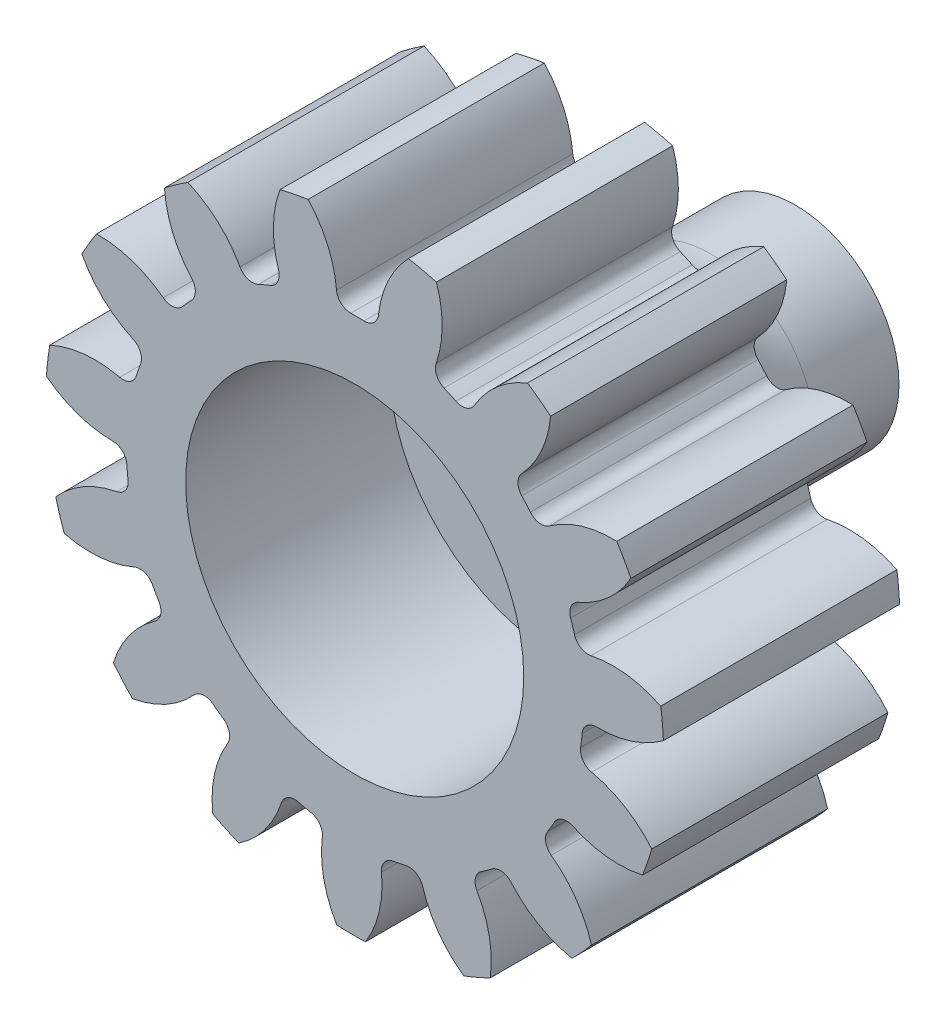
SolidWorks part; units mm, degrees
material "ABS"
ref_plane "Front" through (0, 0, 0) normal (0, 0, 1) x (1, 0, 0)
ref_plane "Top" through (0, 0, 0) normal (0, 1, 0) x (1, 0, 0)
ref_plane "Right" through (0, 0, 0) normal (1, 0, 0) x (0, 0, -1)
sketch "Sketch3" plane through (0, 0, 0) normal (0, 0, 1) x (1, 0, 0)
  circle A0 centre (0, 0) radius 21.59
  dimension "od" = 43.18
extrude "gearBody" add sketch "Sketch3" along normal blind 11
sketch "Sketch2" plane through (0, 0, 0) normal (0, 0, 1) x (1, 0, 0)
  line L0 (0, 0) -> (17.0393, 7.0579) construction
  line L1 (22.0105, -8.0941) -> (0, 0) construction
  line L2 (0, 0) -> (36.3143, 0) construction
  line L3 (19.0486, -0.229) -> (18.5878, -4.1711) construction
  line L5 (18.8182, -2.2) -> (0, 0) construction
  line L7 (0, 0) -> (18.4432, 0) construction
  arc A0 (18.4395, -0.3701) -> (18.0276, -3.8932) centre (0, 0) ccw construction
  arc A1 (21.5666, 1.0048) -> (20.7532, -5.9524) centre (0, 0) ccw construction
  arc A2 (19.0486, -0.229) -> (18.5878, -4.1711) centre (0, 0) ccw construction
  arc A3 (15.7838, -2.3046) -> (15.8898, -1.3984) centre (0, 0) ccw
  arc A4 (22.0105, -8.0941) -> (16.5506, -3.4102) centre (14.9518, -10.798) ccw
  arc A5 (22.0105, -8.0941) -> (23.2839, 2.7987) centre (0, 0) ccw
  arc A6 (23.2839, 2.7987) -> (16.8909, -0.4995) centre (17.0393, 7.0579) cw
  arc A7 (15.8898, -1.3984) -> (16.8909, -0.4995) centre (16.8715, -1.4848) cw
  arc A8 (16.5506, -3.4102) -> (15.7838, -2.3046) centre (16.759, -2.4469) cw
  point P6 (23.2839, 2.7987)
  point P22 (22.0105, -8.0941)
  dimension "baseDia" = 36.8864
  dimension "od" = 43.18
  dimension "pd" = 38.1
  dimension "rd" = 31.9024
  dimension "rFillet" = 0.9855
  dimension "pointX" = 23.2839
  dimension "pointY" = 2.7987
  dimension "CTT" = 3.9421
  dimension "flankCenterAngle" = 22.5
extrude "toothCut" cut sketch "Sketch2" along normal through all
pattern_circular "CirPattern1" count 15 over 360 about axis through (0, 0, 0) along (0, 0, 1) of "toothCut"
scale "Scale1" scale about centroid uniform scaling no x scale factor 0.666667 y scale factor 0.666667 z scale factor 1
sketch "hub1Dia" plane through (0, 0, 0) normal (0, 0, -1) x (-1, 0, 0)
  circle A0 centre (0, 0) radius 12.7
  dimension "hub1Dia" = 25.4
sketch "hub2Dia" plane through (0, 0, 11) normal (0, 0, 1) x (1, 0, 0)
  circle A0 centre (0, 0) radius 12.7
  dimension "hub2dia" = 25.4
sketch "boreDia" plane through (0, 0, 0) normal (0, 0, 1) x (1, 0, 0)
  circle A0 centre (0, 0) radius 7.874
  dimension "boreDia" = 15.748
extrude "bore" cut sketch "boreDia" against normal mid plane 25400
sketch "Sketch4" plane through (0, 0, 0) normal (1, 0, 0) x (0, 0, -1)
  line L0 (9.525, 0) -> (-1.524, 0)
  line L1 (-1.524, 0) -> (-1.524, 7.874)
  line L2 (-1.524, 7.874) -> (0, 7.874)
  line L3 (0, 8.1454) -> (0, 11.133) construction
  line L4 (0, 7.874) -> (0, 10.414)
  line L7 (5.588, 4.826) -> (9.525, 4.826)
  line L8 (9.525, 4.826) -> (9.525, 0)
  line L9 (0, 0) -> (18.4907, 0) construction
  arc A0 (0, 10.414) -> (5.588, 4.826) centre (5.588, 10.414) ccw
  dimension "D2" = 5.588
  dimension "D1" = 15.748
  dimension "D3" = 1.524
  dimension "D5" = 9.652
  dimension "D6" = 9.525
revolve "Revolve1" add sketch "Sketch4" angle 360 about L9
sketch "Sketch5" plane through (0, 0, -9.525) normal (0, 0, -1) x (-1, 0, 0)
  circle A0 centre (0, 0) radius 4.1
  dimension "D1" = 8.2
extrude "Cut-Extrude1" cut sketch "Sketch5" against normal blind 5.3
equation "\"Motor_OD\" = 54.4mm"
equation "\"Motor_Length\" = 401mm"
equation "\"Aft_Section_Length\" = 32in"
equation "\"Mid_Coupler_Length\" = 12in"
equation "\"AB_Coupler_OD_Length\"= 1in"
equation "\"AB_Coupling_Section_Length\"= 0.375in"
equation "\"AB_Coupler_Length\"= \"AB_Coupler_OD_Length\" + \"AB_Coupling_Section_Length\" * 2"
equation "\"Cutout_Angle\" = 60"
equation "\"AB_Paddle_Height\" = 0.375in"
equation "\"AB_Coupler_Num_Screws\"= 4"
equation "\"Num_Cutouts\" = 4"
equation "\"AB_Coupler_OD\"= 4.024in"
equation "\"AB_Coupler_ID\"= 3.7in"
equation "\"AB_Coupler_Surface_Diameter\"= 3.899in"
equation "\"AB_Coupling_Screw_Diameter\"= 4.5mm"
equation "\"AB_Central_Bushing_Length\" = 0.75in"
equation "\"Lead_Screw_Dist\" = 2in"
equation "\"Lead_Screw_Diam\" = 0.375in"
equation "\"Lead_Screw_Length\" = \"Mid_Coupler_Length\" + 2*0.375in + 2*0.5in"
equation "\"Paddle_Pin_Offset\" = 0.25in"
equation "\"Paddle_Pin_Radius\" = 2.25*2/3in"
equation "\"Paddle_Gear_OD\" = 3.2in"
equation "\"Fwd_BKHD_From_Top\" = 18in"
equation "\"Body_Tube_OD\"= 4.024in"
equation "\"Body_Tube_ID\"= 3.90in"
equation "\"Coupler_OD\" = 3.899in"
equation "\"Coupler_ID\" = 3.755in"
equation "\"Fwd_Section_Length\" = 20in"
equation "\"Mid_Section_Length\" = 4in"
equation "\"Aft_Upper_Tube_Length\" = 10in"
equation "\"Aft_Lower_Tube_Length\" = 18in"
equation "\"Nosecone_Coupler_Length\" = 5in"
equation "\"Avionics_Bulkhead_Thickness\" = 0.25in"
equation "\"Avionics_Bulkhead_Lip\" = 0.125in"
equation "\"Avionics_Board_Length\" = \"Mid_Coupler_Length\" - 2*\"Avionics_Bulkhead_Lip\""
equation "\"Lead_Screw_Hole_Diam\" = 0.386in"
equation "\"Centering_Ring_Cutout_Dia\"= 1in"
equation "\"Fin_Thickness\" = 0.118in"
equation "\"Airbrakes_Wire_Hole_Dist\" = 1.1*2/3in"
equation "\"Airbrakes_Wire_Hole_Dia\" = 0.25in"
equation "\"Drive_Gear_OD\" = 1.7*2/3in"
equation "\"DB9_Hole_Dist\" = 25mm"
equation "\"DB9_Relief_Width\" = 0.47in"
equation "\"DB9_Relief_Hole_Offset\" = 0.09in"
equation "\"Servo_Gear_Offset\" = 0.5in"
equation "\"Mounting_Bracket_Centerhole_DIA\" = 0.4in"
equation "\"Drive_Gear_Shaft_DIA\" = \"Mounting_Bracket_Centerhole_DIA\" - 0.02in"
equation "\"Drive_Gear_Fillet\" = 0.22in"
equation "\"Drive_Gear_ID\" = 0.62in"
equation "\"M3_Thread_Clearance\" = 3.8mm"
equation "\"M3_Screw_Head_Diam\" = 6.5mm"
equation "\"Screw_Angle\" = 12.5deg"
equation "\"M3_Insert_OD\" = 4.1mm"
equation "\"M4_Insert_OD\" = 5.5mm"
equation "\"Mounting_Hole_Dist\" = 0.15in"
equation "\"Cam_Slot_Length\" = 7mm"
equation "\"Cam_Slot_Width\" = 10mm"
equation "\"D2@Sketch4\"=\"Drive_Gear_Fillet\""
equation "\"D5@Sketch4\"=\"Drive_Gear_Shaft_DIA\""
equation "\"D1@Sketch4\"=\"Drive_Gear_ID\""
equation "\"Drive_Gear_Offset\" = 0.01in"
